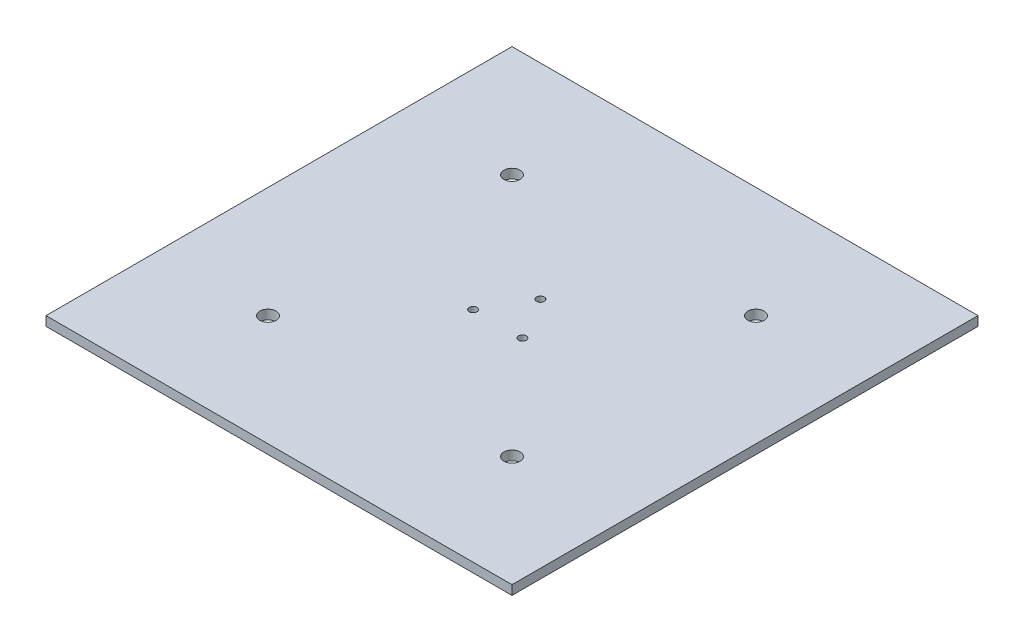
SolidWorks part; units mm, degrees
ref_plane "Front Plane" through (0, 0, 0) normal (0, 0, 1) x (1, 0, 0)
ref_plane "Top Plane" through (0, 0, 0) normal (0, 1, 0) x (1, 0, 0)
ref_plane "Right Plane" through (0, 0, 0) normal (1, 0, 0) x (0, 0, -1)
sketch "Sketch1" plane through (0, 0, 0) normal (0, 1, 0) x (1, 0, 0)
  line L1 (-127, -127) -> (127, -127)
  line L2 (-127, -127) -> (-127, 127)
  line L3 (-127, 127) -> (127, 127)
  line L4 (127, -127) -> (127, 127)
  line L5 (-127, -127) -> (127, 127) construction
  line L6 (-127, 127) -> (127, -127) construction
  point P0 (0, 0)
  dimension "D1" = 254
  dimension "D2" = 254
extrude "Boss-Extrude1" add sketch "Sketch1" along normal blind 5.08
sketch "Sketch2" plane through (0, 5.08, 0) normal (0, 1, 0) x (1, 0, 0)
  line L0 (0, 0) -> (13.4234, -7.75) construction
  line L1 (0, 0) -> (0, 15.5) construction
  line L2 (0, 0) -> (-13.4234, -7.75) construction
  circle A0 centre (0, 0) radius 15.5
  circle A1 centre (0, 15.5) radius 2.1006
  circle A4 centre (13.4234, -7.75) radius 2.1006
  circle A5 centre (-13.4234, -7.75) radius 2.1006
  point P12 (0, 0)
  dimension "D1" = 30.9999
  dimension "D2" = 4.2012
  dimension "D3" = 3
extrude "Cut-Extrude1" cut sketch "Sketch2" against normal through all contours A5 | A4 | A1
sketch "Sketch5" plane through (0, 5.08, 0) normal (0, 1, 0) x (1, 0, 0)
  line L0 (0, 0) -> (69.5783, 63.2721) construction
  circle A0 centre (0, 0) radius 94.0452
  circle A2 centre (66.5427, 66.4573) radius 4.4
  circle A5 centre (66.5427, -66.5427) radius 4.4
  circle A6 centre (-66.4573, -66.5427) radius 4.4
  circle A7 centre (-66.4573, 66.4573) radius 4.4
  point P15 (0.0427, -0.0427)
  dimension "D1" = 188.0904
  dimension "D2" = 4
extrude "Cut-Extrude2" cut sketch "Sketch5" against normal through all
